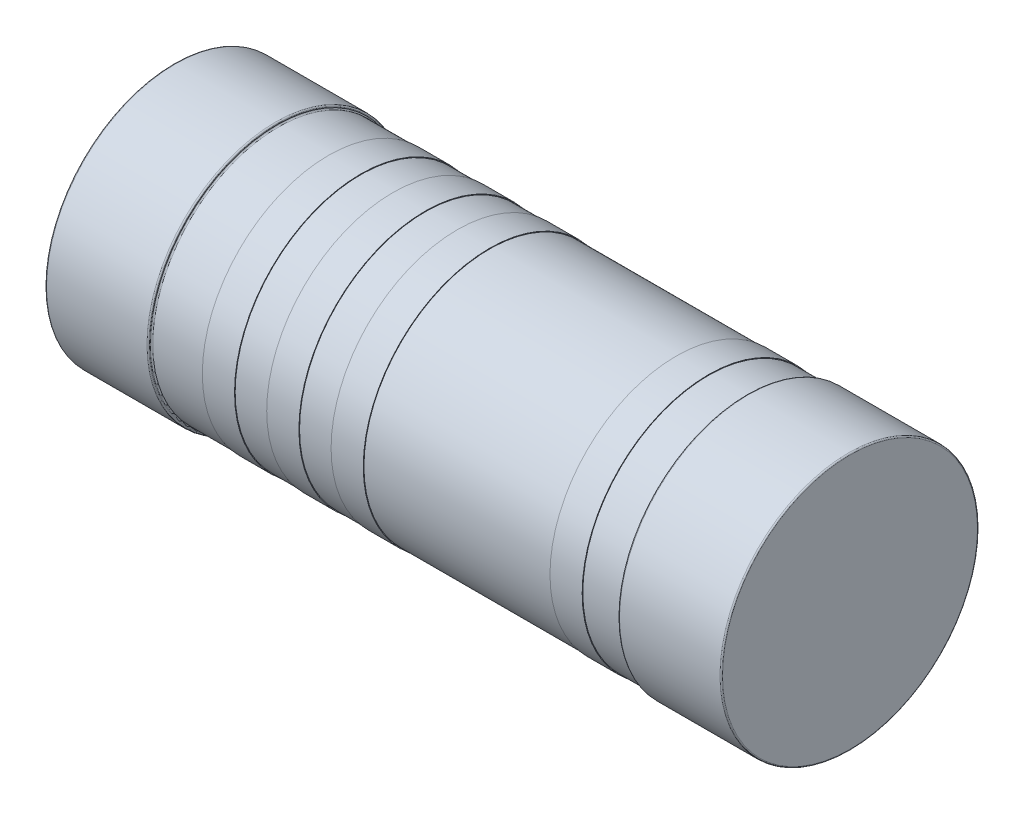
SolidWorks part; units mm, degrees
ref_plane "Front Plane" through (0, 0, 0) normal (0, 0, 1) x (1, 0, 0)
ref_plane "Top Plane" through (0, 0, 0) normal (0, 1, 0) x (1, 0, 0)
ref_plane "Right Plane" through (0, 0, 0) normal (1, 0, 0) x (0, 0, -1)
sketch "Sketch1" plane through (0, 0, 0) normal (0, 0, 1) x (1, 0, 0)
  line L0 (-5.25, 2) -> (5.25, 2)
  line L1 (0, 0) -> (0, 2) construction
  line L2 (-5.25, 2) -> (-3.0256, 2) construction
  line L3 (5.25, 2) -> (5.25, 0.02)
  line L4 (-5.23, 0) -> (-3.67, 0)
  line L5 (-5.25, 0.02) -> (-5.25, 2)
  line L6 (-3.65, 0.02) -> (-3.65, 0.03)
  line L7 (-3.63, 0.05) -> (-2.85, 0.05)
  line L8 (3.65, 0.03) -> (3.65, 0.02)
  line L9 (3.67, 0) -> (5.23, 0)
  line L10 (-2.85, 0.05) -> (-2.85, 0.04)
  line L11 (-2.85, 0.04) -> (-2.35, 0.04)
  line L12 (-2.35, 0.04) -> (-2.35, 0.05)
  line L13 (-1.85, 0.05) -> (-1.85, 0.04)
  line L14 (-1.85, 0.04) -> (-1.35, 0.04)
  line L15 (-1.35, 0.04) -> (-1.35, 0.05)
  line L16 (-0.35, 0.04) -> (-0.85, 0.04)
  line L17 (-0.85, 0.04) -> (-0.85, 0.05)
  line L18 (3.05, 0.05) -> (3.63, 0.05)
  line L19 (-0.35, 0.04) -> (-0.35, 0.05)
  line L20 (3.05, 0.05) -> (3.05, 0.04)
  line L21 (3.05, 0.04) -> (2.55, 0.04)
  line L22 (2.55, 0.04) -> (2.55, 0.05)
  line L23 (-2.6, 0.04) -> (-2.6, -0.0114) construction
  line L24 (-1.6, 0.04) -> (-1.6, -0.0114) construction
  line L25 (-0.6, 0.04) -> (-0.6, -0.0151) construction
  line L26 (2.8, 0.04) -> (2.8, -0.0151) construction
  line L27 (-0.35, 0.05) -> (2.55, 0.05)
  line L28 (-1.35, 0.05) -> (-0.85, 0.05)
  line L29 (-2.35, 0.05) -> (-1.85, 0.05)
  arc A0 (5.25, 0.02) -> (5.23, 0) centre (5.23, 0.02) cw
  arc A1 (3.67, 0) -> (3.65, 0.02) centre (3.67, 0.02) cw
  arc A2 (3.65, 0.03) -> (3.63, 0.05) centre (3.63, 0.03) ccw
  arc A3 (-3.63, 0.05) -> (-3.65, 0.03) centre (-3.63, 0.03) ccw
  arc A4 (-3.65, 0.02) -> (-3.67, 0) centre (-3.67, 0.02) cw
  arc A5 (-5.25, 0.02) -> (-5.23, 0) centre (-5.23, 0.02) ccw
  point P15 (5.25, 0)
  point P18 (3.65, 0)
  dimension "D5" = 0.02
  dimension "D1" = 10.5
  dimension "D2" = 1.6
  dimension "D3" = 0.05
  dimension "D4" = 2
  dimension "D6" = 0.5
  dimension "D7" = 0.01
  dimension "D8" = 1
  dimension "D9" = 1
  dimension "D10" = 0.6
  dimension "D11" = 2.8
revolve "Revolve1" add sketch "Sketch1" angle 360 about L2
